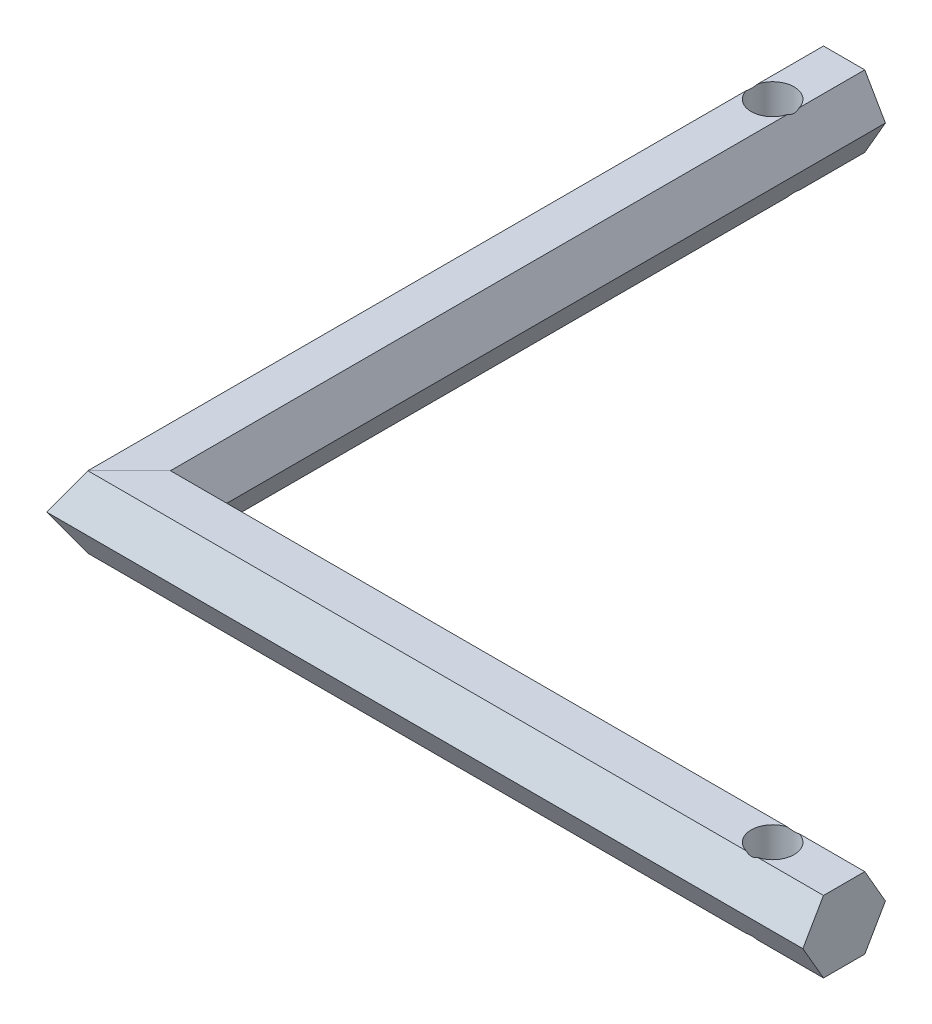
SolidWorks part; units mm, degrees
ref_plane "Plano frontal" through (0, 0, 0) normal (0, 0, 1) x (1, 0, 0)
ref_plane "Plano superior" through (0, 0, 0) normal (0, 1, 0) x (1, 0, 0)
ref_plane "Plano direito" through (0, 0, 0) normal (1, 0, 0) x (0, 0, -1)
sketch "Sketch1" plane through (0, 0, 0) normal (0, 1, 0) x (1, 0, 0)
  line L0 (0, 100) -> (0, 0)
  line L1 (0, 0) -> (100, 0)
  dimension "D1" = 100
  dimension "D2" = 100
ref_plane "Plane1" through (0, 0, -100) normal (0, 0, 1) x (1, 0, 0)
sketch "Sketch2" plane through (0, 0, -100) normal (0, 0, 1) x (1, 0, 0)
  line L0 (0, 0) -> (100, 0) construction
  line L1 (5.7735, 0) -> (2.8868, 5)
  line L2 (2.8868, 5) -> (-2.8868, 5)
  line L3 (-2.8868, 5) -> (-5.7735, 0)
  line L4 (-5.7735, 0) -> (-2.8868, -5)
  line L5 (-2.8868, -5) -> (2.8868, -5)
  line L6 (2.8868, -5) -> (5.7735, 0)
  circle A0 centre (0, 0) radius 5 construction
  point P1 (0, 0)
  dimension "D1" = 10
sweep "Sweep1" add profiles "Sketch2" path "Sketch1"
sketch "Sketch3" plane through (0, 0, 0) normal (0, 1, 0) x (1, 0, 0)
  line L0 (-55, 100) -> (55, 100) construction
  line L1 (100, 2.8868) -> (100, -2.8868) construction
  line L4 (2.8868, 100) -> (-2.8868, 100) construction
  circle A0 centre (0, 90) radius 3
  circle A1 centre (90, 0) radius 3
  point P8 (0, 0)
  point P9 (100, 0)
  point P15 (0, 100)
  dimension "D1" = 6
  dimension "D2" = 6
  dimension "D3" = 10
  dimension "D4" = 10
extrude "Cut-Extrude1" cut sketch "Sketch3" against normal through all both and the other way through all
